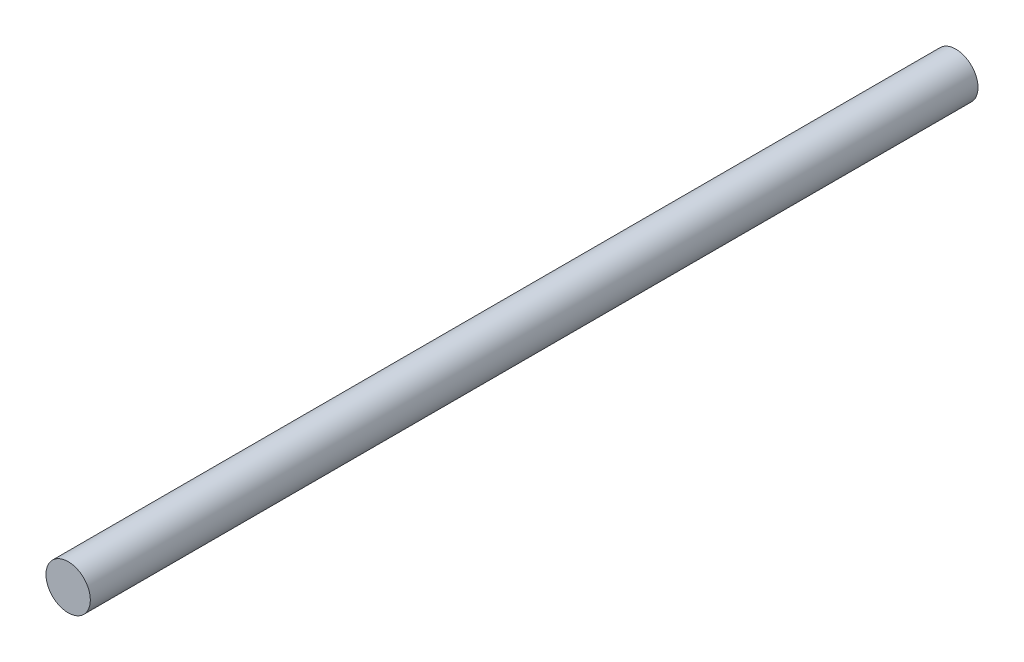
SolidWorks part; units mm, degrees
ref_plane "Front Plane" through (0, 0, 0) normal (0, 0, 1) x (1, 0, 0)
ref_plane "Top Plane" through (0, 0, 0) normal (0, 1, 0) x (1, 0, 0)
ref_plane "Right Plane" through (0, 0, 0) normal (1, 0, 0) x (0, 0, -1)
sketch "Sketch1" plane through (0, 0, 0) normal (0, 0, 1) x (1, 0, 0)
  circle A0 centre (0, 0) radius 1.25
  dimension "D1" = 2.5
extrude "Boss-Extrude1" add sketch "Sketch1" along normal blind 50
